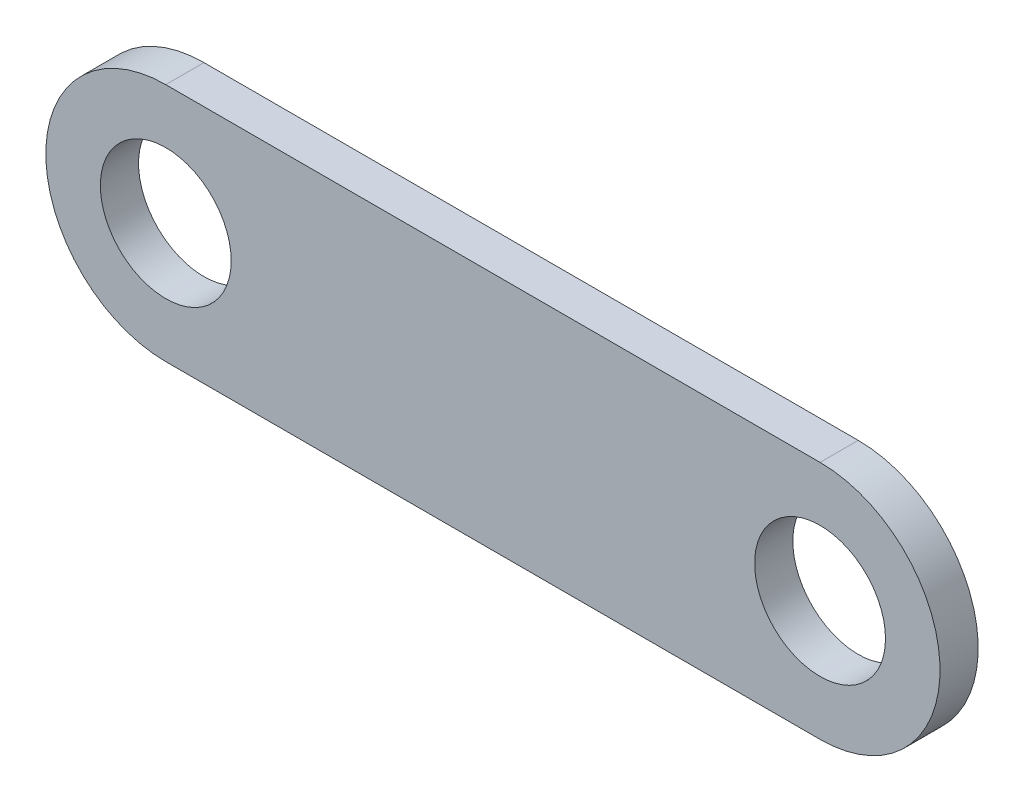
SolidWorks part; units mm, degrees
material "普通碳钢"
ref_plane "前视基准面" through (0, 0, 0) normal (0, 0, 1) x (1, 0, 0)
ref_plane "上视基准面" through (0, 0, 0) normal (0, 1, 0) x (1, 0, 0)
ref_plane "右视基准面" through (0, 0, 0) normal (1, 0, 0) x (0, 0, -1)
sketch "草图1" plane through (0, 0, 0) normal (0, 0, 1) x (1, 0, 0)
  line L0 (30, 0) -> (-30, 0) construction
  line L1 (30, 11) -> (-30, 11)
  line L2 (30, -11) -> (-30, -11)
  circle A0 centre (30, 0) radius 6
  circle A1 centre (-30, 0) radius 6
  arc A2 (30, 11) -> (30, -11) centre (30, 0) cw
  arc A3 (-30, 11) -> (-30, -11) centre (-30, 0) ccw
  point P2 (0, 0)
  point P6 (0, 0)
  dimension "D2" = 12
  dimension "D3" = 12
  dimension "D1" = 60
  dimension "D4" = 11
  dimension "D5" = 11
extrude "凸台-拉伸1" add sketch "草图1" along normal blind 3.5
